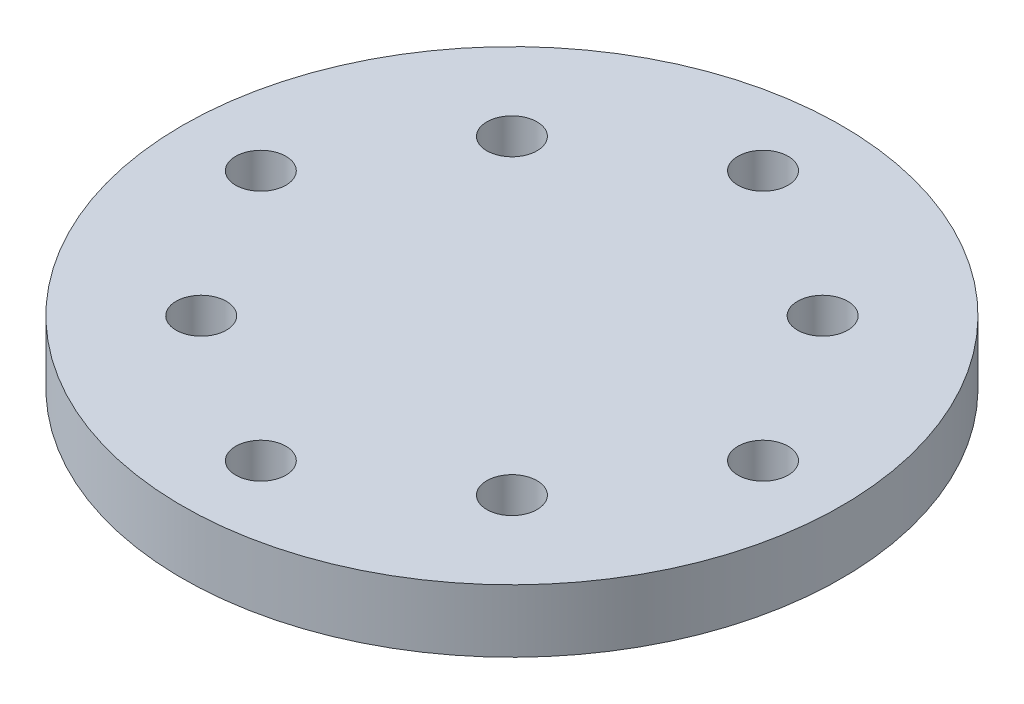
SolidWorks part; units mm, degrees
material "6061 Alloy"
ref_plane "Front Plane" through (0, 0, 0) normal (0, 0, 1) x (1, 0, 0)
ref_plane "Top Plane" through (0, 0, 0) normal (0, 1, 0) x (1, 0, 0)
ref_plane "Right Plane" through (0, 0, 0) normal (1, 0, 0) x (0, 0, -1)
sketch "Sketch1" plane through (0, 0, 0) normal (0, 0, 1) x (1, 0, 0)
  line L0 (-5, 0) -> (-5, 3)
  line L1 (-5, 3) -> (-10.5, 3)
  line L2 (-10.5, 3) -> (-10.5, 5)
  line L3 (-10.5, 5) -> (0, 5)
  line L4 (0, 5) -> (0, 0)
  line L5 (0, 0) -> (-5, 0)
  line L6 (0, 5) -> (0, -17.5943) construction
  dimension "D1" = 21
  dimension "D2" = 10
  dimension "D3" = 2
  dimension "D4" = 5
revolve "Revolve1" add sketch "Sketch1" angle 360 about L6
hole_wizard "M2 Tapped Hole1" positions "Sketch3" profile "Sketch4" tap size "M2" standard "DIN"
sketch "Sketch3" plane through (0, 5, 0) normal (0, 1, 0) x (-1, 0, 0)
  line L1 (-4.9497, 4.9497) -> (4.9497, 4.9497)
  line L2 (-4.9497, 4.9497) -> (-4.9497, -4.9497)
  line L3 (-4.9497, -4.9497) -> (4.9497, -4.9497)
  line L4 (4.9497, 4.9497) -> (4.9497, -4.9497)
  line L5 (-4.9497, 4.9497) -> (4.9497, -4.9497) construction
  line L6 (-4.9497, -4.9497) -> (4.9497, 4.9497) construction
  circle A0 centre (0, 0) radius 7
  circle A1 centre (0, 0) radius 8
  point P0 (-8, 0)
  point P88 (-4.9497, 4.9497)
  dimension "D1" = 16
  dimension "D2" = 14
sketch "Sketch4" plane through (8, 5, 0) normal (1, 0, 0) x (0, 0, 1)
  line L0 (0, 0) -> (0, 6.4807)
  line L1 (0, 6.4807) -> (0.8, 6)
  line L2 (0.8, 6) -> (0.8, 0)
  line L5 (0.8, 0) -> (0, 0)
  line L10 (0, 6.4807) -> (-0.8, 6) construction
  line L11 (0, -6.35) -> (0, 107.95) construction
  dimension "Tap Drill Dia." = 1.6
  dimension "Tap Drill Depth" = 6
  dimension "Drill Angle" = 118
cosmetic thread "Hole Thread1" parameters "D1"=2, "D2"=2
cosmetic thread "Hole Thread2" parameters "D1"=2, "D2"=2
pattern_circular "CirPattern1" count 4 over 360 about axis through (0, 0, 0) along (0, 1, 0) of "M2 Tapped Hole1"
